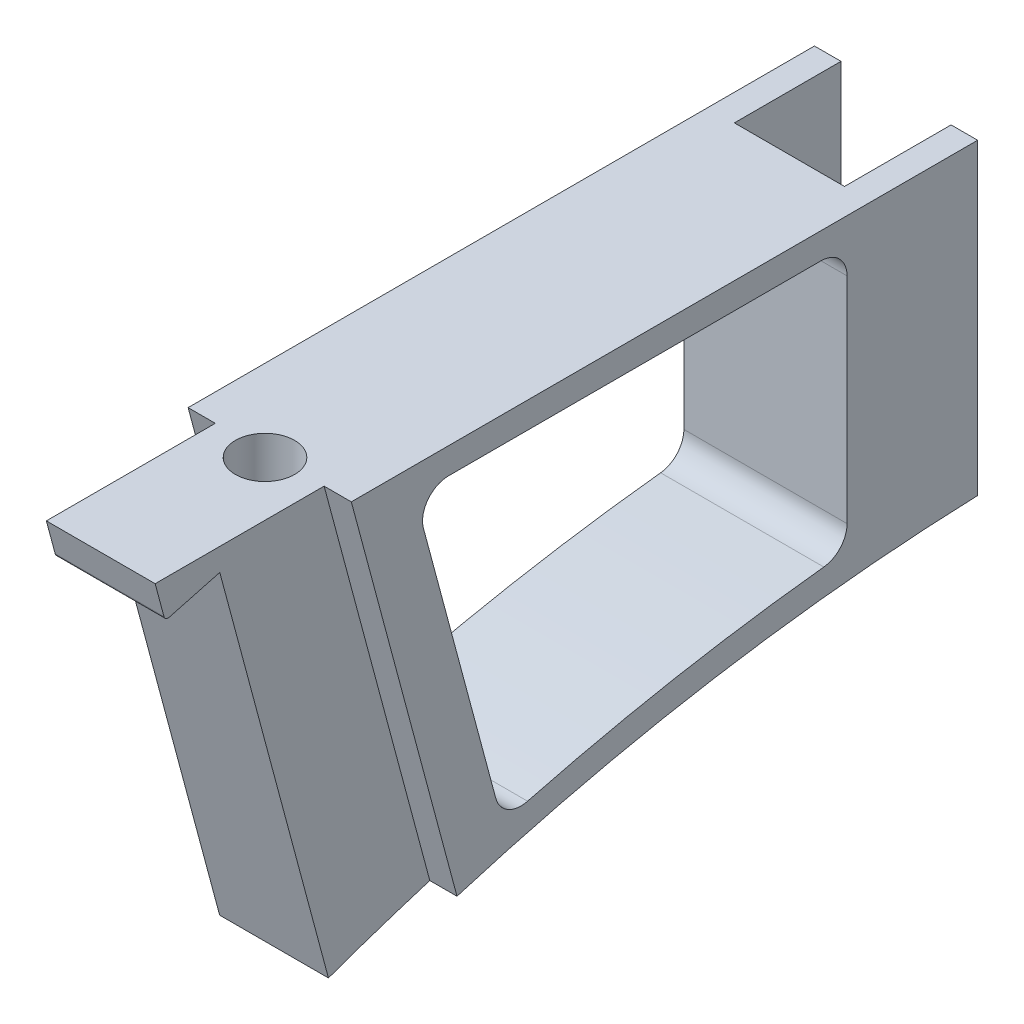
SolidWorks part; units mm, degrees
material "Polyetheretherketone (PEEK)"
ref_plane "Front Plane" through (0, 0, 0) normal (0, 0, 1) x (1, 0, 0)
ref_plane "Top Plane" through (0, 0, 0) normal (0, 1, 0) x (1, 0, 0)
ref_plane "Right Plane" through (0, 0, 0) normal (1, 0, 0) x (0, 0, -1)
sketch "Sketch1" plane through (0, 0, 0) normal (1, 0, 0) x (0, 0, -1)
  line L0 (-18.3899, 0) -> (18.3899, 0)
  line L1 (18.3899, 0) -> (18.3899, -18.354)
  line L2 (-11.6826, -25.032) -> (-18.3899, 0)
  line L3 (0, 0) -> (28.9336, -136.886) construction
  arc A0 (18.3899, -18.354) -> (-11.6826, -25.032) centre (28.9336, -136.886) ccw
  dimension "D5" = 119
  dimension "D1" = 36.7797
  dimension "D2" = 10.5437
  dimension "D3" = 18.354
  dimension "D4" = 15
extrude "Boss-Extrude1" add sketch "Sketch1" along normal mid plane 9.525
hole_wizard "#8-32 Tapped Hole1" positions "Sketch3" profile "Sketch2" tap size "#8-32" standard "ANSI Inch"
sketch "Sketch3" plane through (0, 0, 0) normal (0, 1, 0) x (-1, 0, 0)
  line L0 (0, 18.3899) -> (0, -18.3899) construction
  line L1 (-4.7625, 18.3899) -> (4.7625, 18.3899) construction
  line L2 (-4.7625, -18.3899) -> (4.7625, -18.3899) construction
  point P0 (0, 12.0901)
  dimension "D1" = 30.48
sketch "Sketch2" plane through (0, 0, 12.0901) normal (1, 0, 0) x (0, 0, 1)
  line L0 (0, 0) -> (0, 9.9278)
  line L1 (0, 9.9278) -> (1.7272, 8.89)
  line L2 (1.7272, 8.89) -> (1.7272, 0)
  line L5 (1.7272, 0) -> (0, 0)
  line L10 (0, 9.9278) -> (-1.7272, 8.89) construction
  line L11 (0, -6.35) -> (0, 107.95) construction
  dimension "Tap Drill Dia." = 3.4544
  dimension "Tap Drill Depth" = 8.89
  dimension "Drill Angle" = 118
cosmetic thread "Hole Thread1" parameters "D1"=6.985, "D2"=4.1656
sketch "Sketch4" plane through (4.7625, 0, 0) normal (1, 0, 0) x (0, 0, -1)
  line L0 (18.3899, 0) -> (24.7399, 0)
  line L1 (24.7399, 0) -> (24.7399, -17.9599)
  line L2 (18.3899, -18.354) -> (18.3899, 0) construction
  line L3 (18.3899, -18.354) -> (18.3899, 0)
  arc A0 (18.3899, -18.354) -> (24.7399, -17.9599) centre (28.9336, -136.886) cw
  arc A1 (18.3899, -18.354) -> (-11.6826, -25.032) centre (28.9336, -136.886) ccw construction
  dimension "D1" = 6.35
extrude "Boss-Extrude2" add sketch "Sketch4" against normal up to surface (9.525 mm away) up to face at (-4.7625, -10.6022, -1.6226)
sketch "Sketch5" plane through (0, 0, -24.7399) normal (0, 0, -1) x (-1, 0, 0)
  line L0 (4.7625, 0) -> (-4.7625, 0) construction
  line L1 (-3.2131, 0) -> (3.2131, 0)
  line L2 (-3.2131, 0) -> (-3.2131, -22.225)
  line L3 (-3.2131, -22.225) -> (3.2131, -22.225)
  line L4 (3.2131, 0) -> (3.2131, -22.225)
  line L6 (0, 0) -> (0, -22.225) construction
  dimension "D1" = 6.4262
  dimension "D2" = 22.225
extrude "Cut-Extrude1" cut sketch "Sketch5" against normal blind 6.223
sketch "Sketch6" plane through (4.7625, -3.4556, 12.6767) normal (-1, 0, 0) x (0, -0.263, 0.9648)
  line L1 (4.6032, 4.8365) -> (-1.7394, 3.1075)
  line L2 (-37.0082, -6.5065) -> (4.6032, 4.8365) construction
  line L3 (-1.7394, 3.1075) -> (-1.6362, -20.7257)
  line L4 (4.6032, 4.8365) -> (4.7154, -21.0783)
  line L5 (-32.2848, -23.8342) -> (-37.0082, -6.5065) construction
  arc A1 (4.7154, -21.0783) -> (-32.2848, -23.8342) centre (-5.0537, -139.6766) ccw construction
  arc A2 (4.7154, -21.0783) -> (-1.6362, -20.7257) centre (-5.0537, -139.6766) ccw
  dimension "D1" = 15
  dimension "D2" = 6.35
extrude "Cut-Extrude2" cut sketch "Sketch6" along normal blind 1.5875
mirror "Mirror1" about plane through (0, 0, 0) normal (1, 0, 0) of "Cut-Extrude2"
sketch "Sketch8" plane through (0, 0, 0) normal (1, 0, 0) x (0, 0, -1)
  line L0 (-8.1205, -1.524) -> (17.1199, -1.524)
  line L1 (17.1199, -1.524) -> (17.1199, -16.9424)
  line L2 (-2.9911, -20.667) -> (-8.1205, -1.524)
  line L3 (24.7399, 0) -> (-11.8159, 0) construction
  line L4 (-11.8159, 0) -> (-5.6473, -23.0213) construction
  line L6 (24.7399, -17.9599) -> (24.7399, 0) construction
  arc A0 (17.1199, -16.9424) -> (-2.9911, -20.667) centre (28.9336, -136.886) ccw
  arc A2 (24.7399, -17.9599) -> (-5.6473, -23.0213) centre (28.9336, -136.886) ccw construction
  dimension "D4" = 1.524
  dimension "D1" = 1.524
  dimension "D2" = 7.62
  dimension "D3" = 3.175
extrude "Cut-Extrude4" cut sketch "Sketch8" against normal through all and the other way through all
fillet "Fillet1" radius 1.524 4 edges at (0, -20.667, 2.9911) (0, -16.9424, -17.1199) (0, -1.524, -17.1199) (0, -1.524, 8.1205)
sketch "Sketch9" plane through (3.175, 0, 0) normal (1, 0, 0) x (0, 0, -1)
  line L0 (-18.3899, 0) -> (-21.6769, 0)
  line L1 (-21.6769, 0) -> (-21.0951, -2.1711)
  line L2 (-21.0951, -2.1711) -> (-18.0283, -1.3494)
  line L4 (-11.6826, -25.032) -> (-18.3899, 0) construction
  line L12 (-18.3899, 0) -> (-18.0283, -1.3494)
  dimension "D1" = 1.397
  dimension "D2" = 3.175
extrude "Boss-Extrude3" add sketch "Sketch9" against normal blind 6.35
fillet "Fillet2" radius 0.254 1 edges at (0, -2.1711, 21.0951)
sketch "Sketch12" [suppressed] plane through (0, 0, 0) normal (1, 0, 0) x (0, 0, -1)
  line L0 (19.1939, 0) -> (21.4246, -18.8496)
  line L1 (24.905, 0) -> (-11.99, 0) construction
  line L2 (21.4246, -18.8496) -> (31.896, -18.8496)
  line L3 (31.896, -18.8496) -> (31.896, 0)
  line L4 (31.896, 0) -> (19.1939, 0)
  arc A0 (24.905, -18.5474) -> (-5.4799, -24.813) centre (33.398, -136.5421) ccw construction
sketch "Sketch13" plane through (3.175, 0, 0) normal (1, 0, 0) x (0, 0, -1)
  line L0 (-17.9056, -1.3165) -> (-18.0283, -1.3494)
  line L1 (-18.0283, -1.3494) -> (-11.6826, -25.032)
  line L3 (-11.5627, -24.9885) -> (-17.9056, -1.3165)
  line L4 (-20.8498, -2.1054) -> (-18.0283, -1.3494) construction
  arc A1 (-5.6473, -23.0213) -> (-11.6826, -25.032) centre (28.9336, -136.886) ccw construction
  arc A2 (-11.5627, -24.9885) -> (-11.6826, -25.032) centre (28.9336, -136.886) ccw
  dimension "D1" = 0.127
extrude "Cut-Extrude5" cut sketch "Sketch13" against normal through all
